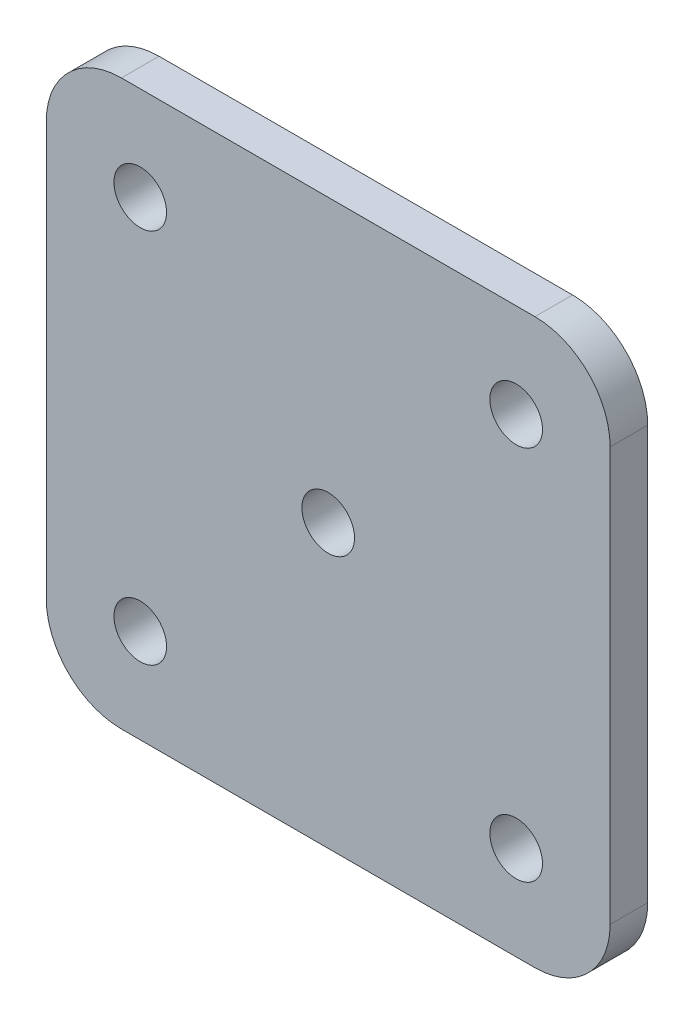
SolidWorks part; units mm, degrees
material "1.0545 (S355N)"
ref_plane "Front Plane" through (0, 0, 0) normal (0, 0, 1) x (1, 0, 0)
ref_plane "Top Plane" through (0, 0, 0) normal (0, 1, 0) x (1, 0, 0)
ref_plane "Right Plane" through (0, 0, 0) normal (1, 0, 0) x (0, 0, -1)
sketch "Sketch1" plane through (0, 0, 0) normal (0, 0, 1) x (1, 0, 0)
  line L0 (-36.5658, 0) -> (63.1228, 0) construction
  line L1 (0, 43.3719) -> (0, -42.4377) construction
  line L2 (-37.5, 37.5) -> (37.5, 37.5)
  line L3 (-37.5, 37.5) -> (-37.5, -37.5)
  line L4 (-37.5, -37.5) -> (37.5, -37.5)
  line L5 (37.5, 37.5) -> (37.5, -37.5)
  dimension "D1" = 75
extrude "Boss-Extrude1" add sketch "Sketch1" along normal blind 5
sketch "Sketch2" plane through (0, 0, 5) normal (0, 0, 1) x (1, 0, 0)
  line L0 (0, 39.5963) -> (0, -41.4866) construction
  line L1 (-42.2825, 0) -> (50.8385, 0) construction
  point P5 (-25, 25)
  point P6 (25, 25)
  point P7 (25, -25)
  point P8 (-25, -25)
  dimension "D1" = 50
  dimension "D2" = 50
hole_wizard "Ø7.0 (7) Diameter Hole2" positions "Sketch3" profile "Sketch4" hole size "Ø7.0" standard "ISO" end condition through all
sketch "Sketch3" plane through (0, 0, 5) normal (0, 0, 1) x (1, 0, 0)
  point P0 (-25, 25)
  point P3 (-25, -25)
  point P6 (25, -25)
  point P9 (25, 25)
sketch "Sketch4" plane through (-25, 25, 5) normal (1, 0, 0) x (0, -1, 0)
  line L0 (0, 0) -> (0, 5)
  line L1 (0, 5) -> (3.5, 5)
  line L2 (3.5, 5) -> (3.5, 0)
  line L5 (3.5, 0) -> (0, 0)
  line L11 (0, -6.35) -> (0, 107.95) construction
  dimension "Thru Hole Dia." = 7
  dimension "Thru Hole Depth" = 5
fillet "Fillet1" radius 10 4 edges at (-37.5, 37.5, 2.5) (-37.5, -37.5, 2.5) (37.5, -37.5, 2.5) (37.5, 37.5, 2.5)
sketch "Sketch5" plane through (0, 0, 5) normal (0, 0, 1) x (1, 0, 0)
  point P0 (0, 0)
hole_wizard "Ø7.0 (7) Diameter Hole1" positions "Sketch8" profile "Sketch7" hole size "Ø7.0" standard "ISO" end condition through all
sketch "Sketch8" plane through (0, 0, 5) normal (0, 0, 1) x (1, 0, 0)
  point P0 (0, 0)
sketch "Sketch7" plane through (0, 0, 5) normal (1, 0, 0) x (0, -1, 0)
  line L0 (0, 0) -> (0, 5)
  line L1 (0, 5) -> (3.5, 5)
  line L2 (3.5, 5) -> (3.5, 0)
  line L5 (3.5, 0) -> (0, 0)
  line L11 (0, -6.35) -> (0, 107.95) construction
  dimension "Thru Hole Dia." = 7
  dimension "Thru Hole Depth" = 5
